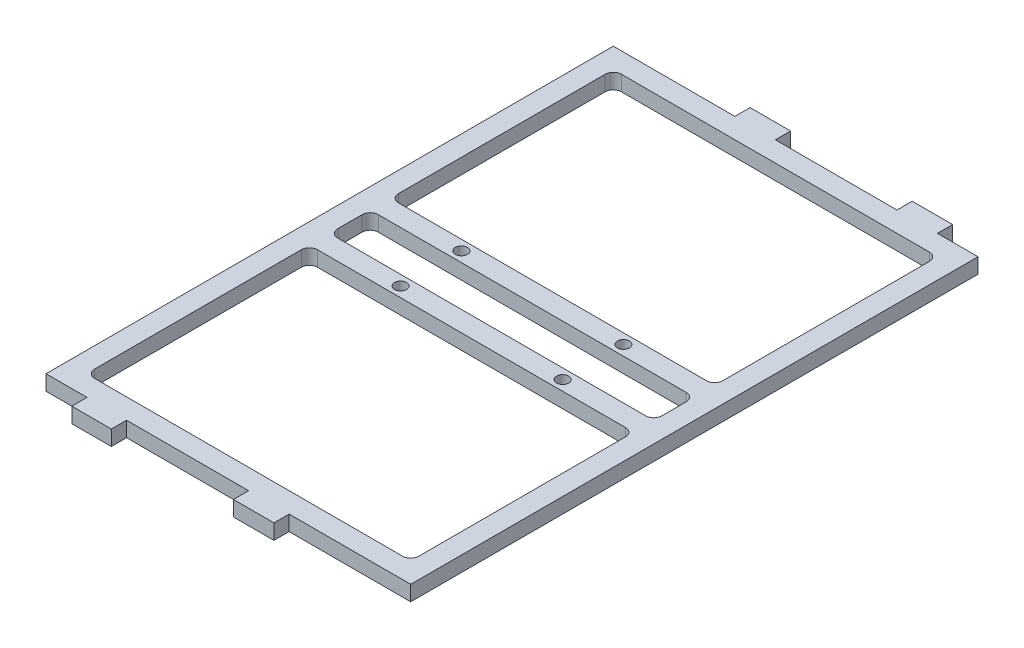
SolidWorks part; units mm, degrees
material "6061-T6 (SS)"
ref_plane "Front Plane" through (0, 0, 0) normal (0, 0, 1) x (1, 0, 0)
ref_plane "Top Plane" through (0, 0, 0) normal (0, 1, 0) x (1, 0, 0)
ref_plane "Right Plane" through (0, 0, 0) normal (1, 0, 0) x (0, 0, -1)
sketch "Sketch1" plane through (0, 0, 0) normal (0, 1, 0) x (1, 0, 0)
  line L0 (50.8, 82.55) -> (-50.8, 82.55)
  line L1 (57.15, 88.9) -> (-57.15, 88.9)
  line L2 (57.15, 88.9) -> (57.15, -88.9)
  line L3 (57.15, -88.9) -> (-57.15, -88.9)
  line L4 (-57.15, 88.9) -> (-57.15, -88.9)
  line L5 (57.15, 88.9) -> (-57.15, -88.9) construction
  line L6 (57.15, -88.9) -> (-57.15, 88.9) construction
  line L7 (-50.8, 82.55) -> (-50.8, -82.55)
  line L8 (50.8, -82.55) -> (-50.8, -82.55)
  line L9 (50.8, 82.55) -> (50.8, -82.55)
  point P0 (0, 0)
  dimension "D1" = 114.3
  dimension "D2" = 177.8
  dimension "D3" = 6.35
extrude "Boss-Extrude1" add sketch "Sketch1" along normal blind 4.7625
sketch "Sketch2" plane through (0, 0, 88.9) normal (0, 0, 1) x (1, 0, 0)
  line L0 (-57.15, 2.3813) -> (57.15, 2.3813) construction
  line L1 (-57.15, 4.7625) -> (-57.15, 0) construction
  line L2 (57.15, 4.7625) -> (57.15, 0) construction
  line L3 (-57.15, 0) -> (57.15, 0) construction
  line L4 (-31.9066, 4.7625) -> (-44.2934, 4.7625)
  line L5 (-31.9066, 4.7625) -> (-31.9066, 0)
  line L6 (-31.9066, 0) -> (-44.2934, 0)
  line L7 (-44.2934, 4.7625) -> (-44.2934, 0)
  line L8 (-31.9066, 4.7625) -> (-44.2934, 0) construction
  line L9 (-31.9066, 0) -> (-44.2934, 4.7625) construction
  line L11 (19.05, 4.7625) -> (6.35, 4.7625)
  line L12 (19.05, 4.7625) -> (19.05, 0)
  line L13 (19.05, 0) -> (6.35, 0)
  line L14 (6.35, 4.7625) -> (6.35, 0)
  line L15 (19.05, 4.7625) -> (6.35, 0) construction
  line L16 (19.05, 0) -> (6.35, 4.7625) construction
  point P6 (-38.1, 2.3813)
  point P13 (12.7, 2.3813)
  dimension "D1" = 19.05
  dimension "D2" = 50.8
  dimension "D3" = 12.7
extrude "Boss-Extrude2" add sketch "Sketch2" along normal blind 4.7625
sketch "Sketch3" plane through (0, 0, -88.9) normal (0, 0, -1) x (-1, 0, 0)
  line L0 (-57.15, 2.3813) -> (57.15, 2.3813) construction
  line L1 (-57.15, 4.7625) -> (-57.15, 0) construction
  line L2 (57.15, 4.7625) -> (57.15, 0) construction
  line L3 (-57.15, 0) -> (57.15, 0) construction
  line L4 (-31.75, 4.7625) -> (-44.45, 4.7625)
  line L5 (-31.75, 4.7625) -> (-31.75, 0)
  line L6 (-31.75, 0) -> (-44.45, 0)
  line L7 (-44.45, 4.7625) -> (-44.45, 0)
  line L8 (-31.75, 4.7625) -> (-44.45, 0) construction
  line L9 (-31.75, 0) -> (-44.45, 4.7625) construction
  line L11 (19.05, 4.7625) -> (6.35, 4.7625)
  line L12 (19.05, 4.7625) -> (19.05, 0)
  line L13 (19.05, 0) -> (6.35, 0)
  line L14 (6.35, 4.7625) -> (6.35, 0)
  line L15 (19.05, 4.7625) -> (6.35, 0) construction
  line L16 (19.05, 0) -> (6.35, 4.7625) construction
  point P6 (-38.1, 2.3812)
  point P13 (12.7, 2.3812)
  dimension "D1" = 12.7
  dimension "D2" = 12.7
  dimension "D3" = 19.05
  dimension "D4" = 50.8
extrude "Boss-Extrude3" add sketch "Sketch3" along normal blind 4.7625
fillet "Fillet1" radius 2.54 4 edges at (50.8, 2.3813, 82.55) (50.8, 2.3813, -82.55) (-50.8, 2.3813, -82.55) (-50.8, 2.3813, 82.55)
sketch "Sketch4" plane through (0, 4.7625, 0) normal (0, 1, 0) x (1, 0, 0)
  line L0 (-57.15, 9.525) -> (57.15, 9.525) construction
  line L1 (-57.15, 88.9) -> (-57.15, -88.9) construction
  line L2 (57.15, -88.9) -> (57.15, 88.9) construction
  line L3 (-57.15, -9.525) -> (57.15, -9.525) construction
  line L5 (50.8, 12.7) -> (-50.8, 12.7)
  line L6 (50.8, 12.7) -> (50.8, 6.35)
  line L7 (50.8, 6.35) -> (-50.8, 6.35)
  line L8 (-50.8, 12.7) -> (-50.8, 6.35)
  line L9 (50.8, 12.7) -> (-50.8, 6.35) construction
  line L10 (50.8, 6.35) -> (-50.8, 12.7) construction
  line L11 (57.15, -6.35) -> (-57.15, -6.35)
  line L12 (57.15, -6.35) -> (57.15, -12.7)
  line L13 (57.15, -12.7) -> (-57.15, -12.7)
  line L14 (-57.15, -6.35) -> (-57.15, -12.7)
  line L15 (57.15, -6.35) -> (-57.15, -12.7) construction
  line L16 (57.15, -12.7) -> (-57.15, -6.35) construction
  point P8 (0, 9.525)
  point P14 (0, -9.525)
  dimension "D1" = 9.525
  dimension "D2" = 9.525
  dimension "D3" = 6.35
  dimension "D4" = 6.35
extrude "Boss-Extrude4" add sketch "Sketch4" against normal blind 4.7625
fillet "Fillet2" radius 2.54 8 edges at (50.8, 2.3813, 6.35) (50.8, 2.3813, -6.35) (-50.8, 2.3813, 6.35) (-50.8, 2.3813, -6.35) (-50.8, 2.3813, 12.7) (50.8, 2.3813, 12.7) (50.8, 2.3813, -12.7) (-50.8, 2.3813, -12.7)
hole_wizard "#6 Clearance Hole1" positions "Sketch6" profile "Sketch5" hole size "#6" standard "Ansi Inch"
sketch "Sketch6" plane through (0, 4.7625, 0) normal (0, 1, 0) x (-1, 0, 0)
  line L1 (-25.4, -9.525) -> (25.4, -9.525)
  line L2 (-25.4, -9.525) -> (-25.4, 9.525)
  line L3 (-25.4, 9.525) -> (25.4, 9.525)
  line L4 (25.4, -9.525) -> (25.4, 9.525)
  line L5 (-25.4, -9.525) -> (25.4, 9.525) construction
  line L6 (-25.4, 9.525) -> (25.4, -9.525) construction
  point P0 (25.4, -9.525)
  point P53 (25.4, 9.525)
  point P55 (-25.4, 9.525)
  point P57 (-25.4, -9.525)
  dimension "D1" = 50.8
  dimension "D2" = 19.05
sketch "Sketch5" plane through (-25.4, 4.7625, -9.525) normal (1, 0, 0) x (0, 0, 1)
  line L0 (0, 0) -> (0, 26.5408)
  line L1 (0, 26.5408) -> (1.8986, 25.4)
  line L2 (1.8986, 25.4) -> (1.8986, 0)
  line L5 (1.8986, 0) -> (0, 0)
  line L10 (0, 26.5408) -> (-1.8986, 25.4) construction
  line L11 (0, -6.35) -> (0, 107.95) construction
  dimension "Hole Dia." = 3.7973
  dimension "Hole Depth" = 25.4
  dimension "Drill Angle" = 118
